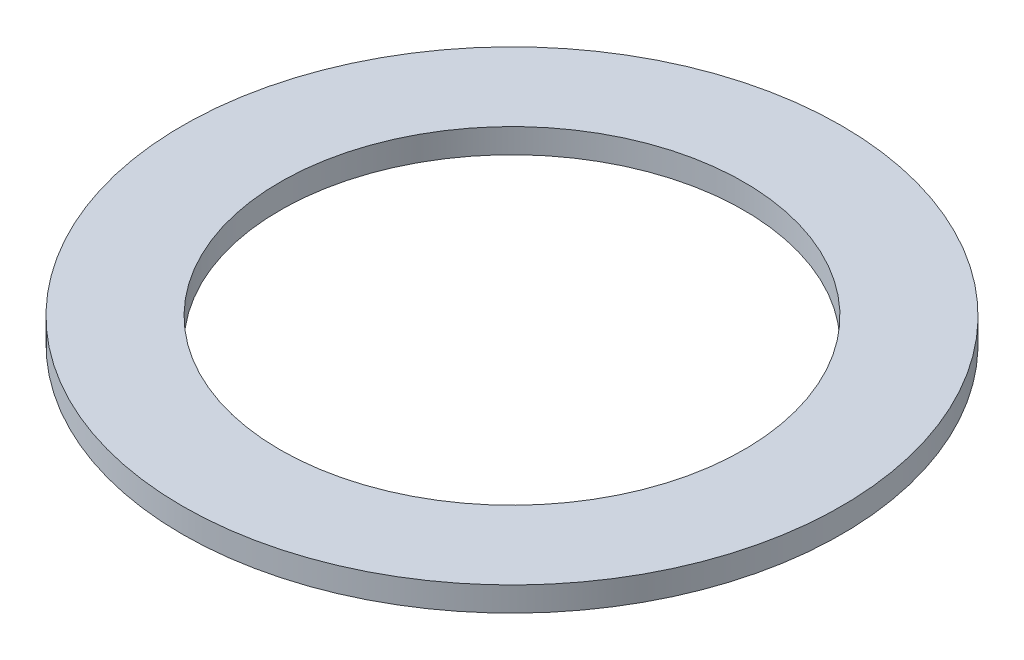
SolidWorks part; units mm, degrees
ref_plane "YZ" through (0, 0, 0) normal (0, 0, 1) x (1, 0, 0)
ref_plane "XY" through (0, 0, 0) normal (0, 1, 0) x (1, 0, 0)
ref_plane "XZ" through (0, 0, 0) normal (1, 0, 0) x (0, 0, -1)
sketch "Sketch1" plane through (0, 0, 0) normal (0, 1, 0) x (1, 0, 0)
  circle A0 centre (0, 0) radius 20.574
  circle A1 centre (0, 0) radius 14.478
  dimension "D1" = 41.148
  dimension "D2" = 28.956
extrude "Base-Extrude" add sketch "Sketch1" along normal blind 1.524
